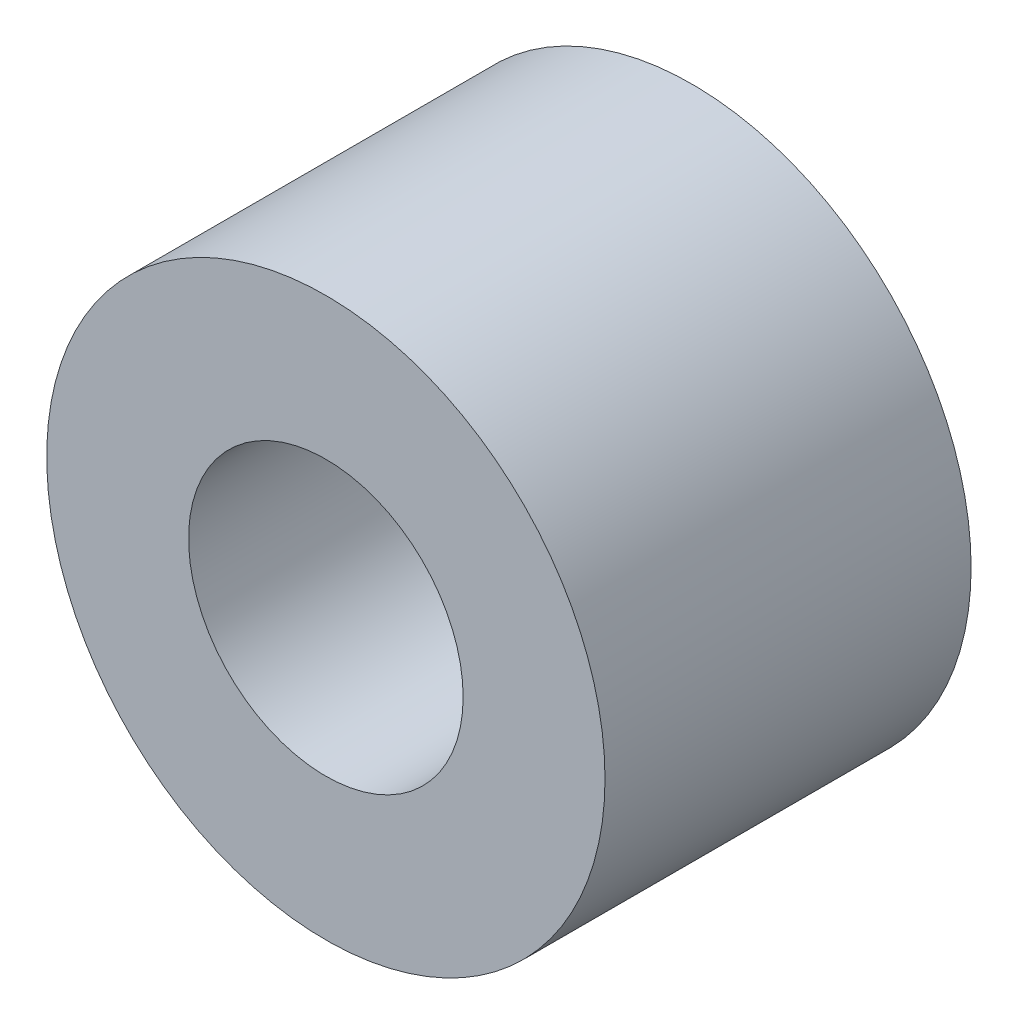
SolidWorks part; units mm, degrees
ref_plane "Alzado" through (0, 0, 0) normal (0, 0, 1) x (1, 0, 0)
ref_plane "Planta" through (0, 0, 0) normal (0, 1, 0) x (1, 0, 0)
ref_plane "Vista lateral" through (0, 0, 0) normal (1, 0, 0) x (0, 0, -1)
sketch "Croquis1" plane through (0, 0, 0) normal (0, 0, 1) x (1, 0, 0)
  circle A0 centre (0, 0) radius 3.05
  circle A1 centre (0, 0) radius 1.5
  dimension "D1" = 6.1
  dimension "D2" = 3
extrude "Saliente-Extruir1" add sketch "Croquis1" along normal blind 4
